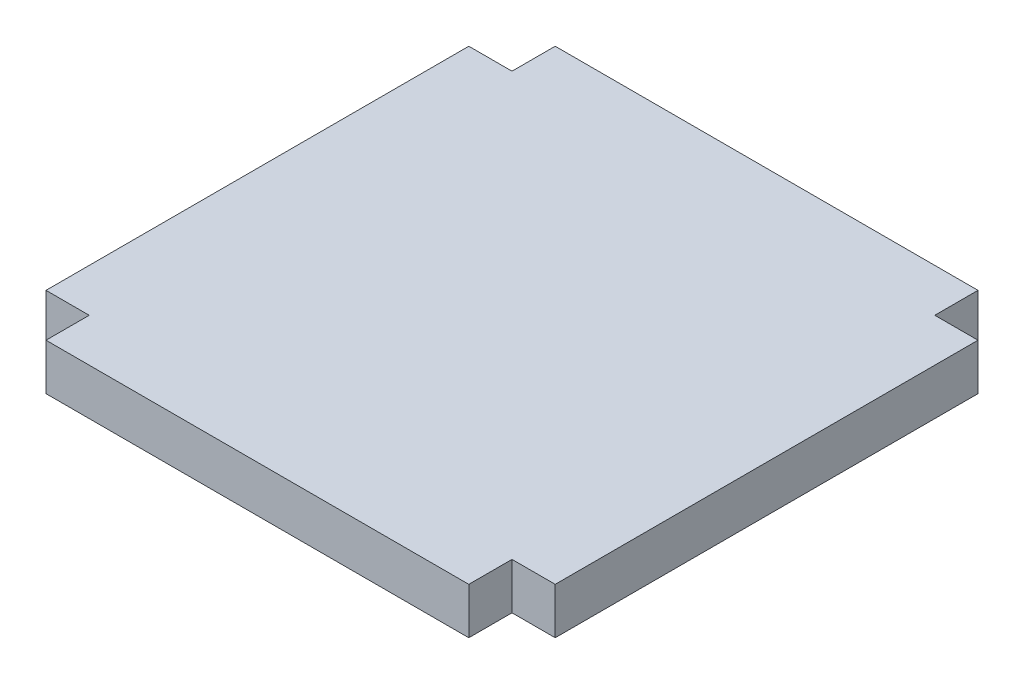
SolidWorks part; units mm, degrees
ref_plane "Front Plane" through (0, 0, 0) normal (0, 0, 1) x (1, 0, 0)
ref_plane "Top Plane" through (0, 0, 0) normal (0, 1, 0) x (1, 0, 0)
ref_plane "Right Plane" through (0, 0, 0) normal (1, 0, 0) x (0, 0, -1)
sketch "Sketch1" plane through (0, 0, 0) normal (0, 1, 0) x (1, 0, 0)
  line L0 (-86.995, 104.775) -> (-86.995, 86.995)
  line L1 (-104.775, -104.775) -> (104.775, -104.775)
  line L2 (-104.775, -104.775) -> (-104.775, 104.775)
  line L3 (-104.775, 104.775) -> (104.775, 104.775)
  line L4 (104.775, -104.775) -> (104.775, 104.775)
  line L5 (-104.775, -104.775) -> (104.775, 104.775) construction
  line L6 (-104.775, 104.775) -> (104.775, -104.775) construction
  line L7 (-86.995, 86.995) -> (-104.775, 86.995)
  line L8 (-86.995, -104.775) -> (-86.995, -86.995)
  line L9 (-86.995, -86.995) -> (-104.775, -86.995)
  line L10 (86.995, -104.775) -> (86.995, -86.995)
  line L11 (86.995, -86.995) -> (104.775, -86.995)
  line L12 (86.995, 104.775) -> (86.995, 86.995)
  line L13 (86.995, 86.995) -> (104.775, 86.995)
  point P0 (0, 0)
  point P8 (-104.775, 0)
  point P10 (0, 104.775)
  dimension "D1" = 209.55
  dimension "D2" = 17.78
extrude "Boss-Extrude1" add sketch "Sketch1" along normal blind 19.05
